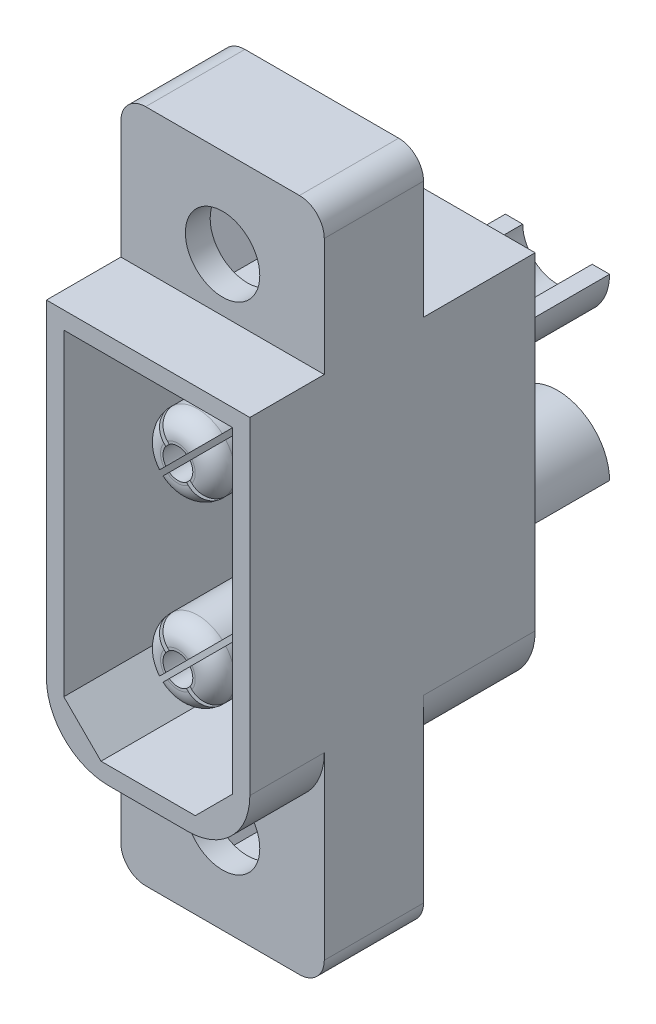
SolidWorks part; units mm, degrees
ref_plane "Front" through (0, 0, 0) normal (0, 0, 1) x (1, 0, 0)
ref_plane "Top" through (0, 0, 0) normal (0, 1, 0) x (1, 0, 0)
ref_plane "Right" through (0, 0, 0) normal (1, 0, 0) x (0, 0, -1)
sketch "Schizzo1" plane through (0, 0, 0) normal (0, 0, 1) x (1, 0, 0)
  line L1 (-3.1, 13.6) -> (3.1, 13.6)
  line L2 (-4.1, 12.6) -> (-4.1, -12.6)
  line L3 (-3.1, -13.6) -> (3.1, -13.6)
  line L4 (4.1, 12.6) -> (4.1, -12.6)
  line L5 (-4.1, 13.6) -> (4.1, -13.6) construction
  line L6 (-4.1, -13.6) -> (4.1, 13.6) construction
  arc A0 (3.1, -13.6) -> (4.1, -12.6) centre (3.1, -12.6) ccw
  arc A1 (-4.1, -12.6) -> (-3.1, -13.6) centre (-3.1, -12.6) ccw
  arc A2 (3.1, 13.6) -> (4.1, 12.6) centre (3.1, 12.6) cw
  arc A3 (-3.1, 13.6) -> (-4.1, 12.6) centre (-3.1, 12.6) ccw
  point P0 (0, 0)
  dimension "D3" = 1
  dimension "D1" = 27.2
  dimension "D2" = 8.2
extrude "Estrusione-Estrusione1" add sketch "Schizzo1" along normal blind 4
sketch "Schizzo2" plane through (0, 0, 4) normal (0, 0, 1) x (1, 0, 0)
  line L2 (-3.1, -13.6) -> (3.1, -13.6) construction
  circle A0 centre (0, 10) radius 1.5
  circle A1 centre (0, -10) radius 1.5
  dimension "D1" = 3
  dimension "D2" = 3
  dimension "D3" = 20
  dimension "D4" = 3.6
extrude "Taglio-Estrusione1" cut sketch "Schizzo2" against normal through all both and the other way through all
sketch "Schizzo4" plane through (0, 0, 4) normal (0, 0, 1) x (1, 0, 0)
  line L0 (4.1, -12.6) -> (4.1, 12.6) construction
  line L1 (-4.1, 7.85) -> (4.1, 7.85)
  line L2 (-4.1, 7.85) -> (-4.1, -5.35)
  line L3 (-1.6, -7.85) -> (1.6, -7.85)
  line L4 (4.1, 7.85) -> (4.1, -5.35)
  line L5 (-4.1, 7.85) -> (4.1, -7.85) construction
  line L6 (-4.1, -7.85) -> (4.1, 7.85) construction
  arc A0 (1.6, -7.85) -> (4.1, -5.35) centre (1.6, -5.35) ccw
  arc A1 (-4.1, -5.35) -> (-1.6, -7.85) centre (-1.6, -5.35) ccw
  point P0 (0, 0)
  dimension "D2" = 2.5
  dimension "D1" = 15.7
extrude "Estrusione-Estrusione3" add sketch "Schizzo4" along normal blind 3
sketch "Schizzo5" plane through (0, 0, 0) normal (0, 0, -1) x (-1, 0, 0)
  line L1 (-1.6, -7.85) -> (1.6, -7.85)
  line L2 (-4.1, -5.35) -> (-4.1, 7.85)
  line L3 (-4.1, 7.85) -> (4.1, 7.85)
  line L4 (4.1, -5.35) -> (4.1, 7.85)
  line L5 (-4.1, -7.85) -> (4.1, 7.85) construction
  line L6 (-4.1, 7.85) -> (4.1, -7.85) construction
  arc A0 (1.6, -7.85) -> (4.1, -5.35) centre (1.6, -5.35) ccw
  arc A1 (-1.6, -7.85) -> (-4.1, -5.35) centre (-1.6, -5.35) cw
  point P0 (0, 0)
  dimension "D1" = 2.5
extrude "Estrusione-Estrusione4" add sketch "Schizzo5" along normal blind 4.5
sketch "Schizzo6" plane through (0, 0, 7) normal (0, 0, 1) x (1, 0, 0)
  line L0 (1.9, -7.15) -> (3.4, -5.65)
  line L1 (-3.4, -5.65) -> (-1.9, -7.15)
  line L8 (-3.4, 7.15) -> (-3.4, -5.35)
  line L9 (-1.6, -7.15) -> (1.6, -7.15)
  line L10 (3.4, -5.35) -> (3.4, 7.15)
  line L11 (3.4, 7.15) -> (-3.4, 7.15)
  line L12 (-3.4, 7.15) -> (-3.4, -5.65)
  line L13 (-1.9, -7.15) -> (1.9, -7.15)
  line L14 (3.4, -5.65) -> (3.4, 7.15)
  line L15 (3.4, 7.15) -> (-3.4, 7.15)
  arc A4 (-3.4, -5.35) -> (-1.6, -7.15) centre (-1.6, -5.35) ccw
  arc A5 (1.6, -7.15) -> (3.4, -5.35) centre (1.6, -5.35) ccw
  point P5 (-3.4, -7.15)
  point P8 (3.4, -7.15)
  dimension "D1" = 0.7
extrude "Taglio-Estrusione2" cut sketch "Schizzo6" against normal blind 9.5
sketch "Schizzo7" plane through (0, 0, -4.5) normal (0, 0, -1) x (-1, 0, 0)
  line L8 (3.4, -5.35) -> (3.4, 7.15)
  line L9 (3.4, 7.15) -> (-3.4, 7.15)
  line L10 (-3.4, 7.15) -> (-3.4, -5.35)
  line L11 (-1.6, -7.15) -> (1.6, -7.15)
  line L12 (3.4, -5.35) -> (3.4, 7.15)
  line L13 (3.4, 7.15) -> (-3.4, 7.15)
  line L14 (-3.4, 7.15) -> (-3.4, -5.35)
  line L15 (-1.6, -7.15) -> (1.6, -7.15)
  arc A4 (-3.4, -5.35) -> (-1.6, -7.15) centre (-1.6, -5.35) ccw
  arc A5 (1.6, -7.15) -> (3.4, -5.35) centre (1.6, -5.35) ccw
  arc A6 (-3.4, -5.35) -> (-1.6, -7.15) centre (-1.6, -5.35) ccw
  arc A7 (1.6, -7.15) -> (3.4, -5.35) centre (1.6, -5.35) ccw
  dimension "D1" = 0.7
extrude "Taglio-Estrusione3" cut sketch "Schizzo7" against normal blind 1
sketch "Schizzo8" plane through (0, 0, -3.5) normal (0, 0, -1) x (-1, 0, 0)
  circle A0 centre (0, -3.6) radius 2.1
  circle A1 centre (0, 3.6) radius 2.1
  dimension "D1" = 4.2
  dimension "D2" = 4.2
  dimension "D3" = 3.6
  dimension "D4" = 7.2
extrude "Estrusione-Estrusione5" add sketch "Schizzo8" along normal blind 6
sketch "Schizzo9" plane through (0, 0, -9.5) normal (0, 0, -1) x (-1, 0, 0)
  line L0 (2.1, 3.6) -> (-2.1, 3.6)
  line L1 (-2.1, 3.6) -> (-2.6336, 3.6)
  line L2 (-2.6336, 3.6) -> (-2.6336, 6.4266)
  line L3 (-2.6336, 6.4266) -> (2.6411, 6.4266)
  line L4 (2.6411, 6.4266) -> (2.6411, 3.6)
  line L5 (2.6411, 3.6) -> (2.1, 3.6)
  line L6 (2.6411, -3.6) -> (-2.6336, -3.6)
  line L7 (-2.6336, -3.6) -> (-2.6336, -6.1075)
  line L8 (-2.6336, -6.1075) -> (2.6411, -6.1075)
  line L9 (2.6411, -6.1075) -> (2.6411, -3.6)
  circle A0 centre (0, 3.6) radius 2.1 construction
  circle A1 centre (0, 3.6) radius 2.1 construction
extrude "Taglio-Estrusione4" cut sketch "Schizzo9" against normal blind 3.2
sketch "Schizzo10" plane through (0, 0, -9.5) normal (0, 0, -1) x (-1, 0, 0)
  line L0 (-2.1, 3.6) -> (2.1, 3.6) construction
  line L1 (2.1, -3.6) -> (-2.1, -3.6) construction
  circle A0 centre (0, 3.6) radius 1.4
  circle A1 centre (0, -3.6) radius 1.4
  dimension "D1" = 2.8
  dimension "D2" = 2.8
extrude "Taglio-Estrusione5" cut sketch "Schizzo10" against normal blind 6
fillet "Raccordo1" radius 1 2 edges at (-1.4, -3.6, -3.5) (-1.4, 3.6, -3.5)
sketch "Schizzo11" plane through (0, 0, -3.5) normal (0, 0, -1) x (-1, 0, 0)
  line L0 (2.6, 1.65) -> (2.6, -1.65)
  line L1 (3.4, -5.35) -> (3.4, 7.15) construction
  line L2 (-3.25, 3.6) -> (-3.2492, -3.5269)
  arc A0 (-3.25, 3.6) -> (2.6, 1.65) centre (0, 3.6) ccw
  arc A1 (2.6, -1.65) -> (-3.2492, -3.5269) centre (0, -3.6) ccw
  dimension "D1" = 6.5
  dimension "D2" = 6.5
  dimension "D3" = 0.8
extrude "Taglio-Estrusione6" cut sketch "Schizzo11" against normal blind 6
sketch "Schizzo12" plane through (0, 0, -2.5) normal (0, 0, 1) x (1, 0, 0)
  circle A0 centre (0, -3.6) radius 1.5
  circle A1 centre (0, 3.6) radius 1.5
  dimension "D1" = 3
  dimension "D2" = 3
extrude "Estrusione-Estrusione6" add sketch "Schizzo12" along normal blind 8.3
fillet "Raccordo2" radius 0.8 2 edges at (1.5, -3.6, 5.8) (1.5, 3.6, 5.8)
sketch "Schizzo14" plane through (0, 0, 5.8) normal (0, 0, 1) x (1, 0, 0)
  line L0 (1.0607, 4.6607) -> (0.4243, 4.0243) construction
  line L1 (1.1314, 2.6101) -> (1.2021, 2.5393)
  line L2 (-1.1314, 4.5899) -> (-0.489, 3.9476)
  line L3 (0.9899, 4.7314) -> (0.3476, 4.089)
  line L4 (-0.9899, 4.7314) -> (-0.3476, 4.089)
  line L5 (1.1314, 4.5899) -> (0.489, 3.9476)
  line L6 (0.4243, 3.1757) -> (1.0607, 2.5393) construction
  line L7 (1.2021, 2.5393) -> (1.0607, 2.3979)
  line L8 (-0.3476, 3.111) -> (-0.9899, 2.4686)
  line L9 (1.1314, 4.5899) -> (-0.9899, 2.4686) construction
  line L10 (0, 3.6) -> (-0.0707, 3.5293) construction
  line L11 (1.0607, 4.6607) -> (-1.0607, 2.5393) construction
  line L12 (-0.489, 3.2524) -> (-1.1314, 2.6101)
  line L13 (0.9899, 4.7314) -> (-1.1314, 2.6101) construction
  line L14 (-0.0707, 3.6707) -> (0, 3.6) construction
  line L15 (0.3476, 3.111) -> (0.9899, 2.4686)
  line L16 (1.0607, 2.3979) -> (0.9899, 2.4686)
  line L17 (1.1314, 4.5899) -> (1.2021, 4.6607)
  line L18 (0.489, 3.2524) -> (1.1314, 2.6101)
  line L19 (1.2021, 4.6607) -> (1.0607, 4.8021)
  line L20 (1.0607, 4.8021) -> (0.9899, 4.7314)
  line L21 (-1.1314, 2.6101) -> (-1.2145, 2.527)
  line L22 (-1.2145, 2.527) -> (-1.0647, 2.3772)
  line L23 (-1.0647, 2.3772) -> (-0.9899, 2.4686)
  line L24 (-0.9899, 4.7314) -> (-1.0647, 4.8061)
  line L25 (-1.0647, 4.8061) -> (-1.2145, 4.6564)
  line L26 (-1.2145, 4.6564) -> (-1.1314, 4.5899)
  line L27 (-0.9899, -2.4686) -> (-0.3476, -3.111)
  line L28 (1.1314, -4.5899) -> (1.2021, -4.6607)
  line L29 (1.0607, -4.8021) -> (0.9899, -4.7314)
  line L30 (-0.489, -3.9476) -> (-1.1314, -4.5899)
  line L31 (-0.3476, -4.089) -> (-0.9899, -4.7314)
  line L32 (1.0607, -2.5393) -> (0.4243, -3.1757) construction
  line L33 (-1.1314, -2.6101) -> (-0.489, -3.2524)
  line L34 (-0.0707, -3.5293) -> (0, -3.6) construction
  line L35 (-1.0647, -2.3939) -> (-1.2145, -2.5436)
  line L36 (0.4243, -4.0243) -> (1.0607, -4.6607) construction
  line L37 (-1.2145, -2.5436) -> (-1.1314, -2.6101)
  line L38 (1.1314, -2.6101) -> (0.489, -3.2524)
  line L39 (1.2021, -4.6607) -> (1.0607, -4.8021)
  line L40 (-1.1314, -4.5899) -> (-1.2145, -4.673)
  line L41 (-0.9899, -2.4686) -> (-1.0647, -2.3939)
  line L42 (1.1314, -2.6101) -> (1.2021, -2.5393)
  line L43 (-1.0647, -4.8228) -> (-0.9899, -4.7314)
  line L44 (0.489, -3.9476) -> (1.1314, -4.5899)
  line L45 (1.2021, -2.5393) -> (1.0607, -2.3979)
  line L46 (0.3476, -4.089) -> (0.9899, -4.7314)
  line L47 (0, -3.6) -> (-0.0707, -3.6707) construction
  line L48 (0.9899, -2.4686) -> (0.3476, -3.111)
  line L49 (1.0607, -2.3979) -> (0.9899, -2.4686)
  line L50 (-1.2145, -4.673) -> (-1.0647, -4.8228)
  arc A0 (0.489, 3.2524) -> (0.489, 3.9476) centre (0, 3.6) ccw
  arc A3 (0.3476, 4.089) -> (-0.3476, 4.089) centre (0, 3.6) ccw
  arc A4 (-0.489, 3.9476) -> (-0.489, 3.2524) centre (0, 3.6) ccw
  arc A5 (-0.3476, 3.111) -> (0.3476, 3.111) centre (0, 3.6) ccw
  arc A6 (-0.3476, -4.089) -> (0.3476, -4.089) centre (0, -3.6) ccw
  arc A7 (0.489, -3.9476) -> (0.489, -3.2524) centre (0, -3.6) ccw
  arc A8 (0.3476, -3.111) -> (-0.3476, -3.111) centre (0, -3.6) ccw
  arc A9 (-0.489, -3.2524) -> (-0.489, -3.9476) centre (0, -3.6) ccw
  dimension "D1" = 1.2
  dimension "D5" = 1.2
  dimension "D3" = 0.1
  dimension "D4" = 0.1
extrude "Taglio-Estrusione7" cut sketch "Schizzo14" against normal blind 7
sketch "Schizzo15" plane through (0, 0, 0) normal (0, 0, -1) x (-1, 0, 0)
  line L1 (2.3671, -10) -> (1.1836, -7.95)
  line L2 (1.1836, -7.95) -> (-1.1836, -7.95)
  line L3 (-1.1836, -7.95) -> (-2.3671, -10)
  line L4 (-2.3671, -10) -> (-1.1836, -12.05)
  line L5 (-1.1836, -12.05) -> (1.1836, -12.05)
  line L6 (1.1836, -12.05) -> (2.3671, -10)
  line L7 (2.3671, 10) -> (1.1836, 12.05)
  line L8 (1.1836, 12.05) -> (-1.1836, 12.05)
  line L9 (-1.1836, 12.05) -> (-2.3671, 10)
  line L10 (-2.3671, 10) -> (-1.1836, 7.95)
  line L11 (-1.1836, 7.95) -> (1.1836, 7.95)
  line L12 (1.1836, 7.95) -> (2.3671, 10)
  circle A0 centre (0, -10) radius 2.05 construction
  circle A1 centre (0, 10) radius 2.05 construction
  dimension "D1" = 4.1
  dimension "D2" = 4.1
extrude "Taglio-Estrusione8" cut sketch "Schizzo15" against normal blind 3
